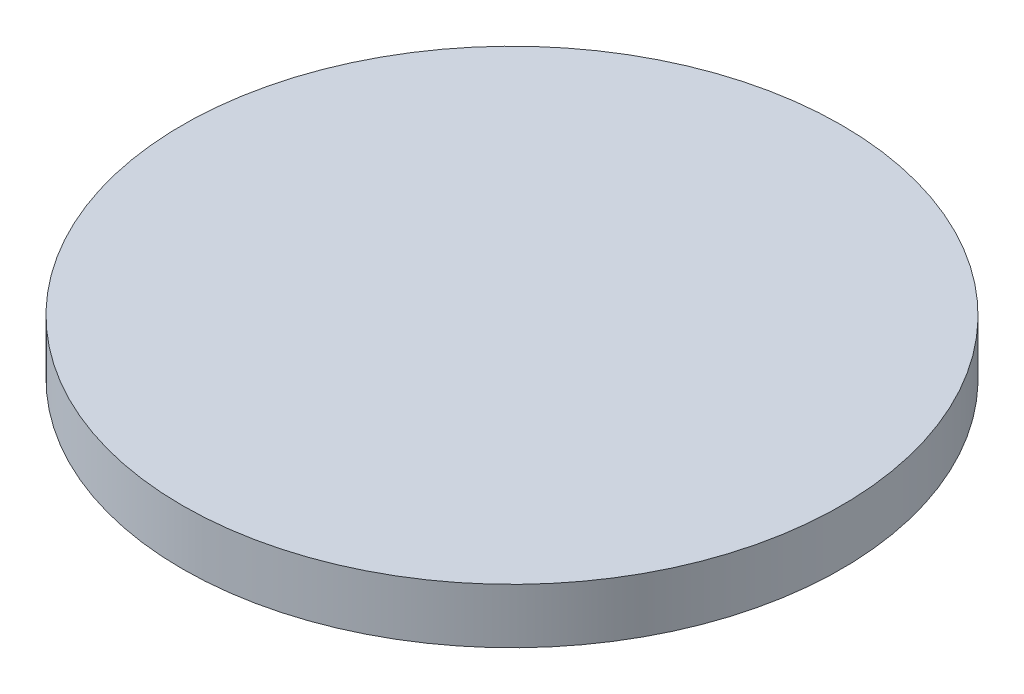
SolidWorks part; units mm, degrees
ref_plane "Front Plane" through (0, 0, 0) normal (0, 0, 1) x (1, 0, 0)
ref_plane "Top Plane" through (0, 0, 0) normal (0, 1, 0) x (1, 0, 0)
ref_plane "Right Plane" through (0, 0, 0) normal (1, 0, 0) x (0, 0, -1)
sketch "Sketch1" plane through (0, 0, 0) normal (0, 1, 0) x (1, 0, 0)
  circle A0 centre (0, 0) radius 38.1
  dimension "D1" = 76.2
extrude "Boss-Extrude1" add sketch "Sketch1" along normal blind 6.35
sketch "Sketch2" plane through (0, 0, 0) normal (0, 0, 1) x (1, 0, 0)
  line L0 (0, 0) -> (0, 158.75) construction
  line L1 (0, 158.75) -> (-11.9995, 127.6892)
  line L2 (-38.1, 6.35) -> (38.1, 6.35)
  spline S0 degree 2 poles (-11.9995, 127.6892) (-1.5692, 89.9344) (-25.0916, 60.8261) knots 0 0 0 1 1 1
  spline S1 degree 2 poles (-25.0916, 60.8261) (-9.6305, 29.5837) (-38.1, 6.35) knots 0 0 0 1 1 1
  spline S2 degree 3 poles (0, 158.75) (0.5433, 129.111) (6.5521, 129.659) (10.9168, 106.6376) (1.1026, 92.7845) (6.7866, 82.4956) knots 0 0 0 0 0.488949 0.588949 1 1 1 1
  spline S3 degree 2 poles (6.7866, 82.4956) (15.5478, 98.7086) (16.4378, 116.9012) knots 0 0 0 1 1 1
  spline S4 degree 3 poles (16.4378, 116.9012) (23.6658, 72.8267) (19.6447, 82.9304) (19.1605, 34.4846) (34.451, 28.9724) (38.1, 6.35) knots 0 0 0 0 0.373034 0.585779 1 1 1 1
  point P9 (21.0536, 47.1079)
  point P12 (23.851, 86.412)
  point P16 (20.0601, 70.0892)
  point P18 (21.2479, 76.9861)
  dimension "D1" = 152.4
  dimension "D2" = 6.7866
  dimension "D3" = 8.8777
  dimension "D4" = 14.6194
  dimension "D5" = 16.4378
  dimension "D6" = 20.0601
  dimension "D7" = 21.0536
  dimension "D8" = 21.2479
  dimension "D9" = 11.8848
  dimension "D10" = 11.9995
  dimension "D11" = 19.9332
  dimension "D12" = 25.0916
  dimension "D13" = 35.3158
  dimension "D14" = 47.1079
  dimension "D15" = 60.8261
  dimension "D16" = 70.0892
  dimension "D17" = 76.9861
  dimension "D18" = 82.4956
  dimension "D19" = 84.9203
  dimension "D20" = 103.3366
  dimension "D21" = 116.9012
  dimension "D22" = 127.6892
sketch "Sketch3" plane through (0, 0, 0) normal (1, 0, 0) x (0, 0, -1)
  line L0 (38.1, 6.35) -> (31.8498, 8.9151)
  line L1 (38.1, 6.35) -> (-38.1, 6.35) construction
  line L2 (31.8498, 8.9151) -> (8.3066, 20.099)
  line L3 (8.3066, 20.099) -> (5.6266, 45.9128)
  line L4 (-10.3105, 121.1851) -> (-21.2771, 156.7744)
  line L5 (-21.2771, 156.7744) -> (-26.0909, 158.75)
  line L6 (-38.1, 6.35) -> (-38.1, 0) construction
  line L7 (38.1, 6.35) -> (-38.1, 6.35)
  spline S0 degree 2 poles (5.6266, 45.9128) (-11.7698, 58.7293) (-10.3105, 121.1851) knots 0 0 0 1 1 1
  spline S1 degree 3 poles (-26.0909, 158.75) (-34.8519, 46.9991) (-7.8994, 18.259) (-38.1, 6.35) knots 0 0 0 0 1 1 1 1
  point P10 (-10.3105, 121.1851)
  point P11 (8.3066, 20.099)
  point P14 (0, 0)
  point P15 (0, 100.9977)
  dimension "D1" = 152.4
  dimension "D2" = 5.6266
  dimension "D3" = 8.3066
  dimension "D4" = 31.8498
  dimension "D5" = 38.1
  dimension "D6" = 10.3105
  dimension "D7" = 21.2771
  dimension "D8" = 26.0909
  dimension "D9" = 8.9151
  dimension "D10" = 20.099
  dimension "D11" = 45.9128
  dimension "D12" = 121.1851
